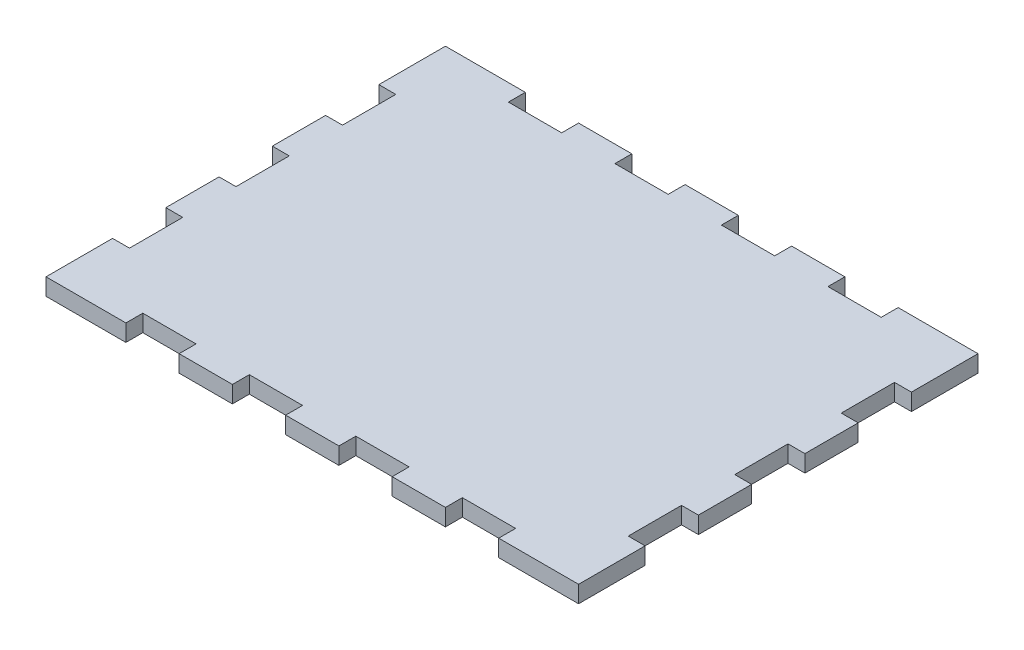
SolidWorks part; units mm, degrees
ref_plane "Front Plane" through (0, 0, 0) normal (0, 0, 1) x (1, 0, 0)
ref_plane "Top Plane" through (0, 0, 0) normal (0, 1, 0) x (1, 0, 0)
ref_plane "Right Plane" through (0, 0, 0) normal (1, 0, 0) x (0, 0, -1)
sketch "Sketch1" plane through (0, 0, 0) normal (0, 1, 0) x (1, 0, 0)
  line L0 (110, 0) -> (110, 6.35)
  line L1 (0, 0) -> (200, 0)
  line L2 (0, 0) -> (0, 150)
  line L3 (0, 150) -> (200, 150)
  line L4 (200, 0) -> (200, 150)
  line L5 (30, 0) -> (50, 0)
  line L6 (30, 0) -> (30, 6.35)
  line L7 (30, 6.35) -> (50, 6.35)
  line L8 (50, 0) -> (50, 6.35)
  line L9 (70, 0) -> (90, 0)
  line L10 (70, 0) -> (70, 6.35)
  line L11 (70, 6.35) -> (90, 6.35)
  line L12 (90, 0) -> (90, 6.35)
  line L13 (110, 0) -> (130, 0)
  line L14 (130, 0) -> (130, 6.35)
  line L15 (110, 6.35) -> (130, 6.35)
  line L16 (150, 0) -> (150, 6.35)
  line L17 (150, 0) -> (170, 0)
  line L18 (170, 0) -> (170, 6.35)
  line L19 (150, 6.35) -> (170, 6.35)
  line L20 (0, 75) -> (200, 75) construction
  line L21 (150, 150) -> (170, 150)
  line L22 (170, 150) -> (170, 143.65)
  line L23 (150, 143.65) -> (170, 143.65)
  line L24 (150, 150) -> (150, 143.65)
  line L25 (110, 150) -> (130, 150)
  line L26 (130, 150) -> (130, 143.65)
  line L27 (110, 143.65) -> (130, 143.65)
  line L28 (110, 150) -> (110, 143.65)
  line L29 (70, 143.65) -> (90, 143.65)
  line L30 (90, 150) -> (90, 143.65)
  line L31 (70, 150) -> (90, 150)
  line L32 (70, 150) -> (70, 143.65)
  line L33 (30, 143.65) -> (50, 143.65)
  line L34 (50, 150) -> (50, 143.65)
  line L35 (30, 150) -> (50, 150)
  line L36 (30, 150) -> (30, 143.65)
  line L37 (0, 65) -> (0, 85)
  line L38 (0, 25) -> (6.35, 25)
  line L39 (0, 25) -> (0, 45)
  line L40 (0, 45) -> (6.35, 45)
  line L41 (6.35, 25) -> (6.35, 45)
  line L42 (0, 65) -> (6.35, 65)
  line L43 (6.35, 65) -> (6.35, 85)
  line L44 (0, 85) -> (6.35, 85)
  line L45 (0, 105) -> (0, 125)
  line L46 (0, 105) -> (6.35, 105)
  line L47 (6.35, 105) -> (6.35, 125)
  line L48 (0, 125) -> (6.35, 125)
  line L49 (100, 0) -> (100, 150) construction
  line L62 (200, 105) -> (193.65, 105)
  line L63 (193.65, 105) -> (193.65, 125)
  line L64 (200, 125) -> (193.65, 125)
  line L65 (200, 105) -> (200, 125)
  line L66 (200, 65) -> (193.65, 65)
  line L67 (193.65, 65) -> (193.65, 85)
  line L68 (200, 85) -> (193.65, 85)
  line L69 (200, 65) -> (200, 85)
  line L70 (200, 45) -> (193.65, 45)
  line L71 (193.65, 25) -> (193.65, 45)
  line L72 (200, 25) -> (193.65, 25)
  line L73 (200, 25) -> (200, 45)
  dimension "D1" = 200
  dimension "D2" = 150
  dimension "D3" = 10
  dimension "D4" = 20
  dimension "D5" = 6.35
  dimension "D6" = 20
  dimension "D7" = 20
  dimension "D8" = 6.35
  dimension "D10" = 20
  dimension "D11" = 10
  dimension "D12" = 20
  dimension "D13" = 6.35
  dimension "D15" = 20
  dimension "D9" = 3
  dimension "D14" = 3
extrude "Boss-Extrude1" add sketch "Sketch1" along normal blind 6.35 contours L72 L4 L3 L22 L23 L24 L26 L27 L28 L30 L29 L32 L34 L33 L36 L2 L48 L47 L46 L44 L43 L42 L40 L41 L38 L1 L6 L7 L8 L10 L11 L12 L0 L15 L14 L16 L19 L18 L64
